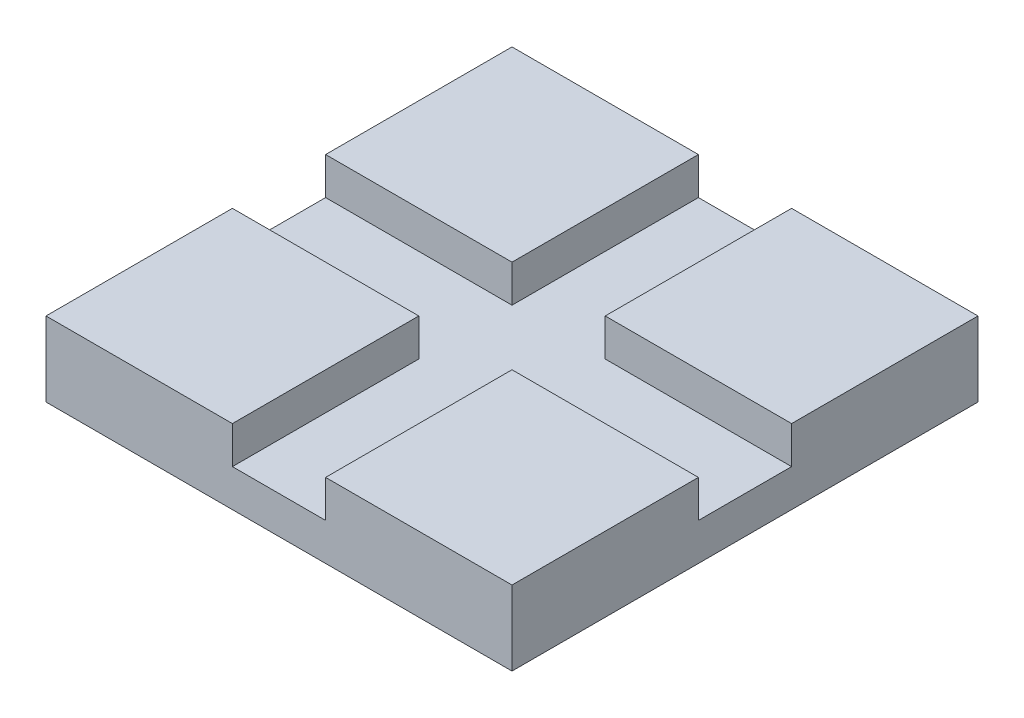
SolidWorks part; units mm, degrees
ref_plane "Front Plane" through (0, 0, 0) normal (0, 0, 1) x (1, 0, 0)
ref_plane "Top Plane" through (0, 0, 0) normal (0, 1, 0) x (1, 0, 0)
ref_plane "Right Plane" through (0, 0, 0) normal (1, 0, 0) x (0, 0, -1)
sketch "Sketch1" plane through (0, 0, 0) normal (0, 1, 0) x (1, 0, 0)
  line L1 (-12.5, 12.5) -> (12.5, 12.5)
  line L2 (-12.5, 12.5) -> (-12.5, -12.5)
  line L3 (-12.5, -12.5) -> (12.5, -12.5)
  line L4 (12.5, 12.5) -> (12.5, -12.5)
  line L5 (-12.5, 12.5) -> (12.5, -12.5) construction
  line L6 (-12.5, -12.5) -> (12.5, 12.5) construction
  point P0 (0, 0)
  dimension "D1" = 25
extrude "Boss-Extrude1" add sketch "Sketch1" along normal blind 2
sketch "Sketch2" plane through (0, 2, 0) normal (0, 1, 0) x (1, 0, 0)
  line L0 (-12.5, -12.5) -> (12.5, -12.5) construction
  line L1 (12.5, -12.5) -> (2.5, -12.5)
  line L2 (12.5, -12.5) -> (12.5, -2.5)
  line L3 (12.5, -2.5) -> (2.5, -2.5)
  line L4 (2.5, -12.5) -> (2.5, -2.5)
  line L5 (-12.5, -12.5) -> (-2.5, -12.5)
  line L6 (-12.5, -12.5) -> (-12.5, -2.5)
  line L7 (-12.5, -2.5) -> (-2.5, -2.5)
  line L8 (-2.5, -12.5) -> (-2.5, -2.5)
  line L9 (-12.5, 12.5) -> (-12.5, -12.5) construction
  line L11 (-12.5, 12.5) -> (-2.5, 12.5)
  line L12 (-12.5, 12.5) -> (-12.5, 2.5)
  line L13 (-12.5, 2.5) -> (-2.5, 2.5)
  line L14 (-2.5, 12.5) -> (-2.5, 2.5)
  line L15 (12.5, 12.5) -> (2.5, 12.5)
  line L16 (12.5, 12.5) -> (12.5, 2.5)
  line L17 (12.5, 2.5) -> (2.5, 2.5)
  line L18 (2.5, 12.5) -> (2.5, 2.5)
  dimension "D1" = 10
extrude "Boss-Extrude4" add sketch "Sketch2" along normal blind 2
equation "\"topSize\"=25"
equation "\"D1@Sketch1\"= \"topSize\""
equation "\"notchSize\"=10"
equation "\"D1@Sketch2\"=\"notchSize\""
equation "\"notchHeight\"=2"
equation "\"D1@Boss-Extrude4\"=\"notchHeight\""
equation "\"D1@Sketch1\"=\"topSize\""
